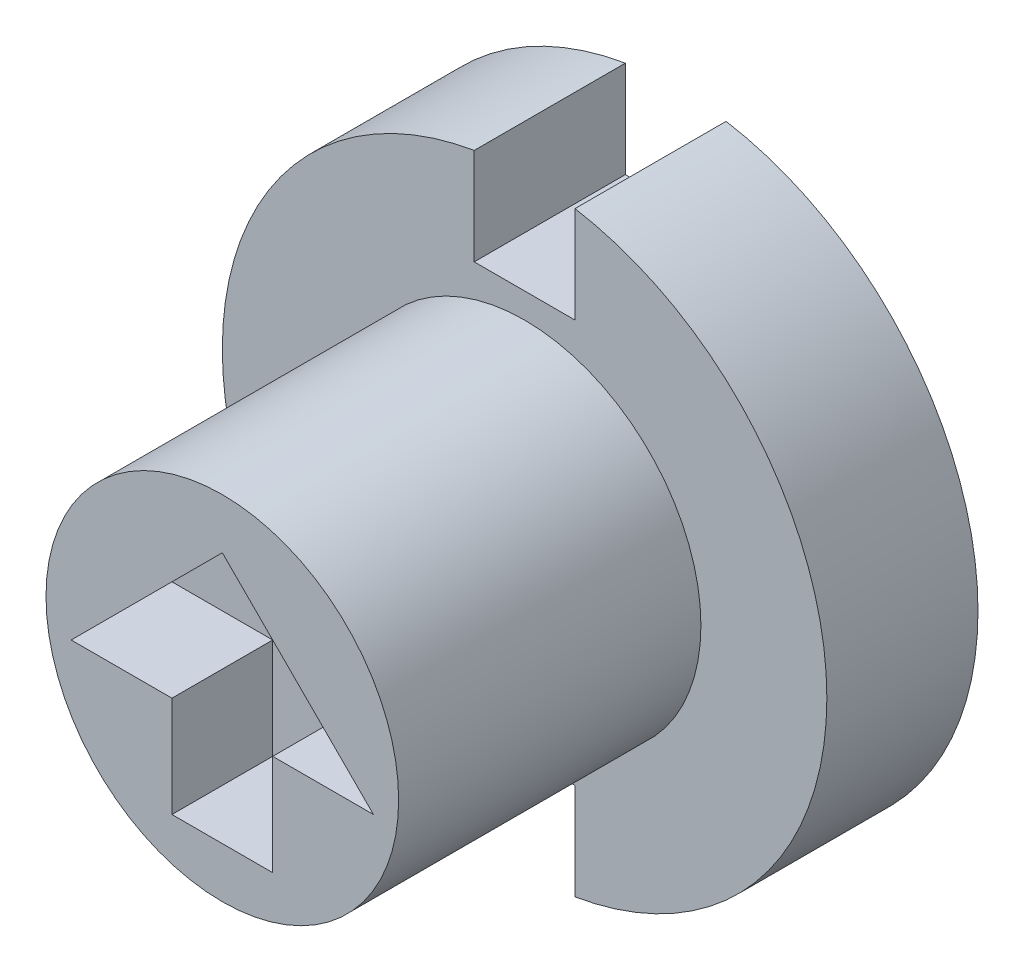
SolidWorks part; units mm, degrees
material "Caucho"
ref_plane "Alzado" through (0, 0, 0) normal (0, 0, 1) x (1, 0, 0)
ref_plane "Planta" through (0, 0, 0) normal (0, 1, 0) x (1, 0, 0)
ref_plane "Vista lateral" through (0, 0, 0) normal (1, 0, 0) x (0, 0, -1)
sketch "Croquis1" plane through (0, 0, 0) normal (0, 0, 1) x (1, 0, 0)
  circle A0 centre (-4.7541, 3.9783) radius 3.5
  dimension "D1" = 7
extrude "Saliente-Extruir1" add sketch "Croquis1" along normal blind 6
sketch "Croquis2" plane through (0, 0, 0) normal (0, 0, -1) x (-1, 0, 0)
  circle A0 centre (4.7541, 3.9783) radius 6
  dimension "D1" = 12
extrude "Saliente-Extruir2" add sketch "Croquis2" along normal blind 3
sketch "Croquis3" plane through (0, 0, 6) normal (0, 0, 1) x (1, 0, 0)
  line L0 (-4.7541, 7.4783) -> (-4.7541, 0.4783) construction
  line L1 (-5.7541, 1.4783) -> (-3.7541, 1.4783)
  line L2 (-3.7541, 1.4783) -> (-3.7541, 3.4783)
  line L3 (-5.7541, 1.4783) -> (-5.7541, 3.4783)
  line L4 (-3.7541, 3.4783) -> (-1.7541, 3.4783)
  line L5 (-5.7541, 3.4783) -> (-7.7541, 3.4783)
  line L6 (-1.7541, 3.4783) -> (-4.7541, 6.4783)
  line L7 (-7.7541, 3.4783) -> (-4.7541, 6.4783)
  circle A0 centre (-4.7541, 3.9783) radius 3.5 construction
  circle A1 centre (-4.7541, 3.9783) radius 3.5 construction
  point P10 (-4.7541, 1.4783)
  dimension "D1" = 1
  dimension "D2" = 1
  dimension "D3" = 2
  dimension "D4" = 2
  dimension "D5" = 3
extrude "Cortar-Extruir1" cut sketch "Croquis3" against normal blind 2
sketch "Croquis4" plane through (0, 0, 0) normal (0, 0, 1) x (1, 0, 0)
  line L0 (-4.7541, 9.9783) -> (-4.7541, -2.0217) construction
  line L1 (-5.7541, 7.9783) -> (-3.7541, 7.9783)
  line L2 (-3.7541, 7.9783) -> (-3.7541, 9.9783)
  line L3 (-5.7541, 7.9783) -> (-5.7541, 9.9783)
  line L4 (-3.7541, 9.9783) -> (-5.7541, 9.9783)
  line L5 (-5.7541, -0.0217) -> (-3.7541, -0.0217)
  line L6 (-3.7541, -0.0217) -> (-3.7541, -2.0217)
  line L7 (-5.7541, -0.0217) -> (-5.7541, -2.0217)
  line L8 (-3.7541, -2.0217) -> (-4.7541, -2.0217)
  line L9 (-5.7541, -2.0217) -> (-4.7541, -2.0217)
  circle A0 centre (-4.7541, 3.9783) radius 6 construction
  circle A2 centre (-4.7541, 3.9783) radius 3.5 construction
  circle A3 centre (-4.7541, 3.9783) radius 3.5 construction
  point P8 (-4.7541, 7.9783)
  point P10 (-4.7541, 9.9783)
  point P14 (-4.7541, -0.0217)
  dimension "D1" = 2
  dimension "D2" = 2
  dimension "D3" = 2
  dimension "D4" = 2
  dimension "D5" = 4
  dimension "D6" = 4
extrude "Cortar-Extruir2" cut sketch "Croquis4" against normal through all
